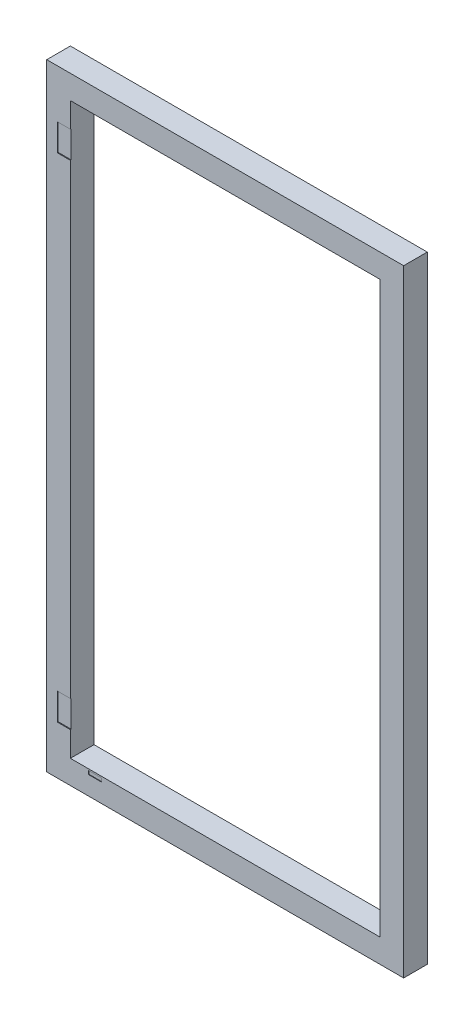
SolidWorks part; units mm, degrees
ref_plane "Front Plane" through (0, 0, 0) normal (0, 0, 1) x (1, 0, 0)
ref_plane "Top Plane" through (0, 0, 0) normal (0, 1, 0) x (1, 0, 0)
ref_plane "Right Plane" through (0, 0, 0) normal (1, 0, 0) x (0, 0, -1)
sketch "Sketch1" plane through (0, 0, 0) normal (0, 0, 1) x (1, 0, 0)
  line L1 (-11.9336, 2359.2382) -> (1298.0664, 2359.2382)
  line L2 (-11.9336, 2359.2382) -> (-11.9336, -50.7618)
  line L3 (-11.9336, -50.7618) -> (1298.0664, -50.7618)
  line L4 (1298.0664, 2359.2382) -> (1298.0664, -50.7618)
  line L5 (-111.9336, 2459.2382) -> (1398.0664, 2459.2382)
  line L6 (-111.9336, 2459.2382) -> (-111.9336, -150.7618)
  line L7 (-111.9336, -150.7618) -> (1398.0664, -150.7618)
  line L8 (1398.0664, 2459.2382) -> (1398.0664, -150.7618)
  dimension "D1" = 2410
  dimension "D2" = 1310
  dimension "D3" = 100
  dimension "D4" = 100
  dimension "D5" = 100
  dimension "D6" = 100
extrude "Boss-Extrude1" add sketch "Sketch1" along normal blind 100
sketch "Sketch2" plane through (0, 0, 100) normal (0, 0, 1) x (1, 0, 0)
  line L0 (-11.9336, 2359.2382) -> (-11.9336, -50.7618) construction
  line L1 (-67.4336, 2254.2382) -> (-11.9336, 2254.2382)
  line L2 (-67.4336, 2254.2382) -> (-67.4336, 2140.2382)
  line L3 (-67.4336, 2140.2382) -> (-11.9336, 2140.2382)
  line L4 (-11.9336, 2254.2382) -> (-11.9336, 2140.2382)
  line L5 (1298.0664, 2359.2382) -> (-11.9336, 2359.2382) construction
  line L6 (-11.9336, 168.2382) -> (-67.4336, 168.2382)
  line L7 (-11.9336, 168.2382) -> (-11.9336, 54.2382)
  line L8 (-11.9336, 54.2382) -> (-67.4336, 54.2382)
  line L9 (-67.4336, 168.2382) -> (-67.4336, 54.2382)
  line L10 (-11.9336, -50.7618) -> (1298.0664, -50.7618) construction
  dimension "D1" = 105
  dimension "D2" = 105
  dimension "D3" = 114
  dimension "D4" = 55.5
  dimension "D5" = 55.5
  dimension "D6" = 114
extrude "Cut-Extrude1" cut sketch "Sketch2" against normal blind 3.4
sketch "Sketch4" plane through (0, 0, 100) normal (0, 0, 1) x (1, 0, 0)
  line L2 (64.7841, -64.4198) -> (64.7841, -71.9198)
  line L3 (-11.9336, -50.7618) -> (1298.0664, -50.7618) construction
  line L8 (64.7841, -56.9198) -> (119.7841, -56.9198)
  line L9 (64.7841, -71.9198) -> (72.2841, -71.9198)
  line L11 (72.2841, -71.9198) -> (114.2245, -71.9198) construction
  line L12 (72.2841, -71.9198) -> (114.2245, -71.9198)
  line L15 (64.7841, -56.9198) -> (64.7841, -64.4198)
  line L19 (119.7841, -56.9198) -> (119.7841, -71.9198)
  line L20 (119.7841, -71.9198) -> (114.2245, -71.9198)
  dimension "D1" = 6.158
  dimension "D2" = 15
  dimension "D3" = 55
extrude "Cut-Extrude2" cut sketch "Sketch4" against normal blind 2
sketch "Sketch6" plane through (0, 0, 0) normal (0, 0, -1) x (-1, 0, 0)
  line L0 (-1342.0866, 2459.2382) -> (-1342.0866, -150.7618) construction
  line L1 (-1398.0664, 2459.2382) -> (111.9336, 2459.2382) construction
  line L2 (111.9336, -150.7618) -> (-1398.0664, -150.7618) construction
  line L4 (-1393.0664, 1229.2382) -> (-1303.0664, 1229.2382)
  line L6 (-1393.0664, 1079.2382) -> (-1303.0664, 1079.2382)
  line L9 (-1393.0664, 1229.2382) -> (-1393.0664, 1079.2382)
  line L10 (-1303.0664, 1229.2382) -> (-1303.0664, 1079.2382)
  line L11 (-1398.0664, -150.7618) -> (-1398.0664, 2459.2382) construction
  line L12 (-1298.0664, -50.7618) -> (-1298.0664, 2359.2382) construction
  point P10 (-1342.0866, 1154.2382)
  dimension "D1" = 5
  dimension "D2" = 5
  dimension "D3" = 75
  dimension "D4" = 150
extrude "Cut-Extrude3" cut sketch "Sketch6" against normal blind 81
sketch "Sketch8" plane through (0, 0, 0) normal (0, 0, -1) x (-1, 0, 0)
  line L0 (-1353.3164, 1104.7382) -> (-1342.8164, 1104.7382)
  line L1 (-1393.0664, 1229.2382) -> (-1303.0664, 1229.2382)
  line L2 (-1393.0664, 1229.2382) -> (-1393.0664, 1079.2382)
  line L3 (-1393.0664, 1079.2382) -> (-1303.0664, 1079.2382)
  line L4 (-1303.0664, 1229.2382) -> (-1303.0664, 1079.2382)
  line L5 (-1353.3164, 1104.7382) -> (-1353.3164, 1094.2382)
  line L6 (-1353.3164, 1094.2382) -> (-1342.8164, 1094.2382)
  line L7 (-1342.8164, 1104.7382) -> (-1342.8164, 1094.2382)
  dimension "D1" = 10.5
  dimension "D2" = 10.5
  dimension "D3" = 39.75
  dimension "D4" = 15
extrude "Boss-Extrude6" add sketch "Sketch8" against normal blind 0.01 separate body
